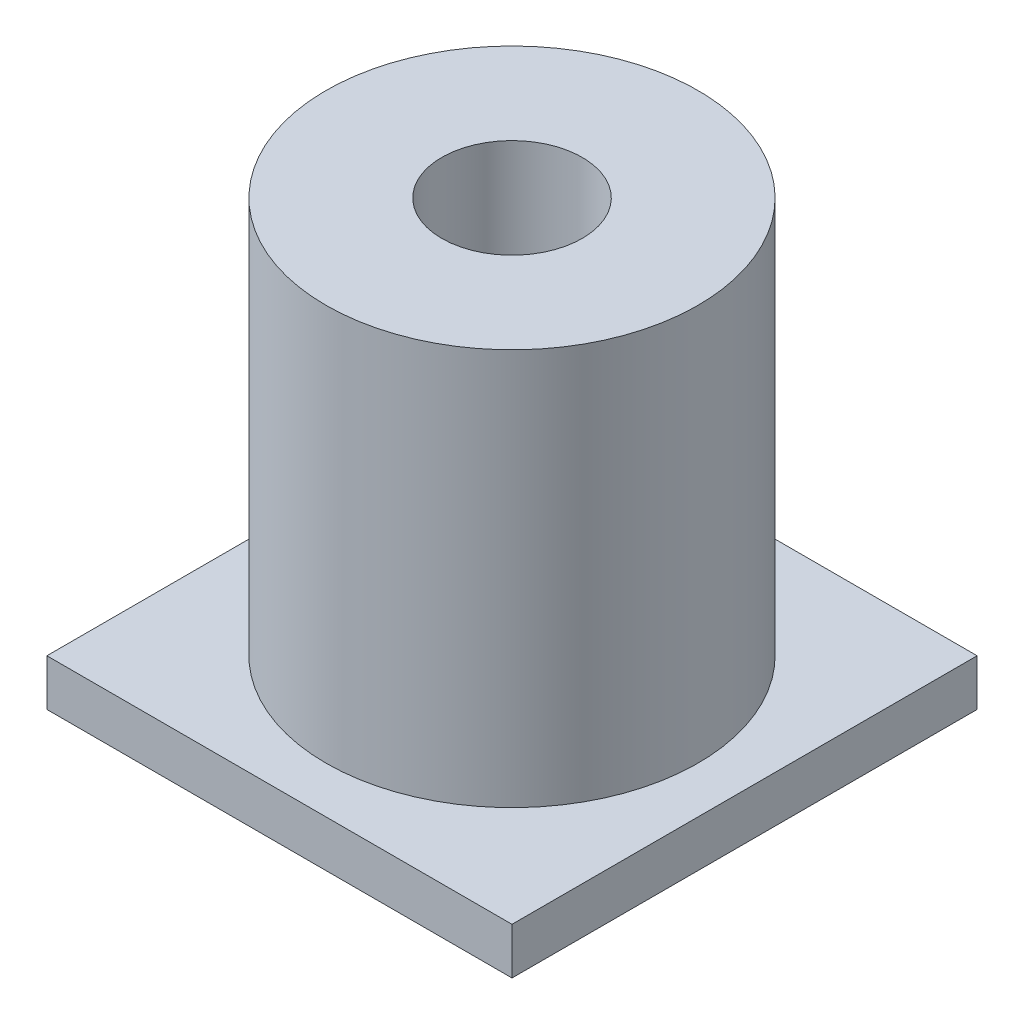
SolidWorks part; units mm, degrees
ref_plane "Front Plane" through (0, 0, 0) normal (0, 0, 1) x (1, 0, 0)
ref_plane "Top Plane" through (0, 0, 0) normal (0, 1, 0) x (1, 0, 0)
ref_plane "Right Plane" through (0, 0, 0) normal (1, 0, 0) x (0, 0, -1)
sketch "Sketch1" plane through (0, 0, 0) normal (0, 1, 0) x (1, 0, 0)
  line L1 (0, 0) -> (10, 0)
  line L2 (0, 0) -> (0, -10)
  line L3 (0, -10) -> (10, -10)
  line L4 (10, 0) -> (10, -10)
  circle A0 centre (5, -5) radius 1.25
  point P8 (5, 0)
  point P10 (0, -5)
  dimension "D3" = 2.5
  dimension "D1" = 10
  dimension "D2" = 10
extrude "Boss-Extrude1" add sketch "Sketch1" along normal blind 1
sketch "Sketch2" plane through (0, 1, 0) normal (0, 1, 0) x (1, 0, 0)
  circle A0 centre (5, -5) radius 1.51
  circle A1 centre (5, -5) radius 1.25 construction
  circle A2 centre (5, -5) radius 4
  dimension "D1" = 3.02
  dimension "D2" = 8
extrude "Boss-Extrude2" add sketch "Sketch2" along normal blind 8.525
